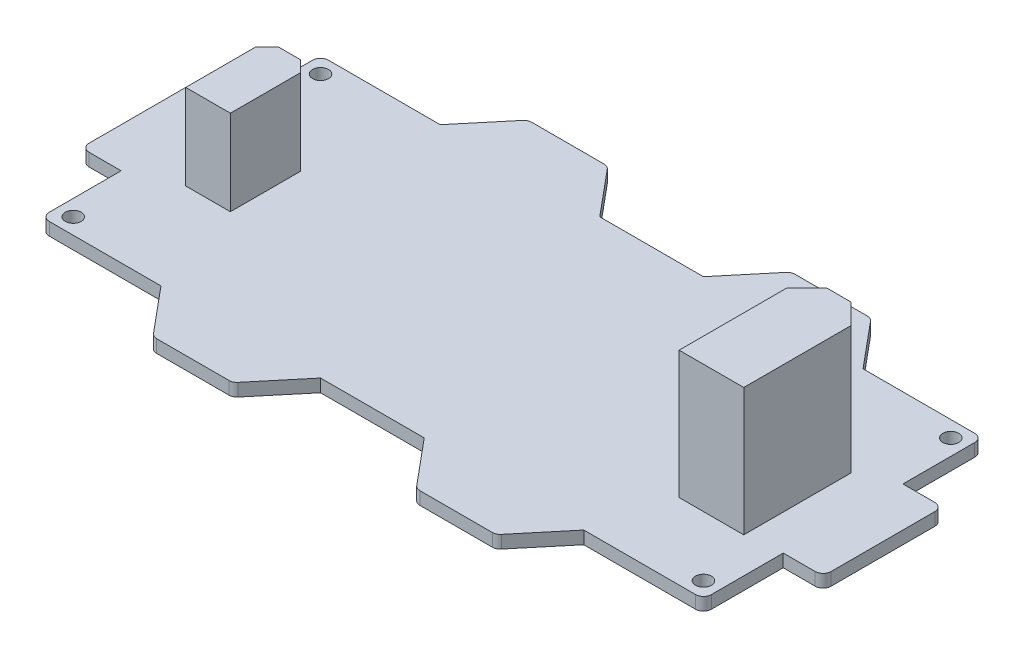
SolidWorks part; units mm, degrees
ref_plane "前视基准面" through (0, 0, 0) normal (0, 0, 1) x (1, 0, 0)
ref_plane "上视基准面" through (0, 0, 0) normal (0, 1, 0) x (1, 0, 0)
ref_plane "右视基准面" through (0, 0, 0) normal (1, 0, 0) x (0, 0, -1)
other "Configuration Table"
sketch "草图1" plane through (0, 0, 0) normal (0, 1, 0) x (1, 0, 0)
  line L0 (-26.5, 17.5) -> (-21.5, 23.5)
  line L1 (-41.5, -17.5) -> (-26.5, -17.5)
  line L2 (-41.5, -17.5) -> (-41.5, -7.5)
  line L3 (-41.5, 17.5) -> (-26.5, 17.5)
  line L4 (41.5, -17.5) -> (41.5, 17.5) construction
  line L5 (0, 17.5) -> (0, -17.5) construction
  line L6 (-41.5, 0) -> (41.5, 0) construction
  line L7 (-21.5, 23.5) -> (-11.5, 23.5)
  line L8 (-11.5, 23.5) -> (-6.5, 17.5)
  line L9 (-11.5, -23.5) -> (-6.5, -17.5)
  line L10 (-21.5, -23.5) -> (-11.5, -23.5)
  line L11 (-26.5, -17.5) -> (-21.5, -23.5)
  line L12 (21.5, -23.5) -> (11.5, -23.5)
  line L13 (11.5, -23.5) -> (6.5, -17.5)
  line L14 (26.5, -17.5) -> (21.5, -23.5)
  line L15 (11.5, 23.5) -> (6.5, 17.5)
  line L16 (21.5, 23.5) -> (11.5, 23.5)
  line L17 (26.5, 17.5) -> (21.5, 23.5)
  line L18 (-6.5, 17.5) -> (6.5, 17.5)
  line L19 (26.5, 17.5) -> (41.5, 17.5)
  line L20 (-6.5, -17.5) -> (6.5, -17.5)
  line L21 (26.5, -17.5) -> (41.5, -17.5)
  line L22 (-41.5, 7.5) -> (-41.5, 17.5)
  line L23 (-46.5, -7.5) -> (-41.5, -7.5)
  line L24 (-46.5, -7.5) -> (-46.5, 7.5)
  line L25 (-46.5, 7.5) -> (-41.5, 7.5)
  line L27 (-41.5, 7.5) -> (-41.5, -7.5) construction
  line L28 (-46.5, 0) -> (-36.5, 0) construction
  line L29 (46.5, 7.5) -> (41.5, 7.5)
  line L30 (46.5, -7.5) -> (41.5, -7.5)
  line L31 (46.5, -7.5) -> (46.5, 7.5)
  line L32 (41.5, -7.5) -> (41.5, -17.5)
  line L33 (41.5, 7.5) -> (41.5, 17.5)
  circle A0 centre (-39.5, 15.5) radius 1
  circle A1 centre (-39.5, -15.5) radius 1
  circle A2 centre (39.5, -15.5) radius 1
  circle A3 centre (39.5, 15.5) radius 1
  point P0 (0, 0)
  dimension "D9" = 2
  dimension "D1" = 15
  dimension "D2" = 35
  dimension "D3" = 20
  dimension "D4" = 5
  dimension "D5" = 6
  dimension "D6" = 10
  dimension "D7" = 15
  dimension "D8" = 83
  dimension "D10" = 2
  dimension "D11" = 2
extrude "PCB" add sketch "草图1" along normal blind 1.6
sketch "板上孔" plane through (0, 1.6, 0) normal (0, 1, 0) x (1, 0, 0)
  line L0 (0, -61.9012) -> (0, 61.9012) construction
  line L1 (-109.9353, 0) -> (109.9353, 0) construction
  line L2 (-14, -28) -> (14, -28) construction
  line L3 (-14, 33.5) -> (14, 33.5) construction
  line L4 (-14, 33.5) -> (-14, 22.5) construction
  line L5 (-14, 22.5) -> (14, 22.5) construction
  line L6 (14, 33.5) -> (14, 22.5) construction
  line L7 (0, 22.5) -> (0, 33.5) construction
  line L8 (-14, 28) -> (14, 28) construction
  line L9 (0, -22.5) -> (0, -33.5) construction
  line L10 (14, -33.5) -> (14, -22.5) construction
  line L11 (-14, -22.5) -> (14, -22.5) construction
  line L12 (-14, -33.5) -> (-14, -22.5) construction
  line L13 (-14, -33.5) -> (14, -33.5) construction
  line L14 (38, 0) -> (28, 0) construction
  line L15 (-38, -14) -> (-28, -14) construction
  line L16 (-38, -14) -> (-38, 14) construction
  line L17 (-38, 14) -> (-28, 14) construction
  line L18 (-28, -14) -> (-28, 14) construction
  line L19 (-33, 14) -> (-33, -14) construction
  line L20 (-38, 0) -> (-28, 0) construction
  line L21 (33, 14) -> (33, -14) construction
  line L22 (28, -14) -> (28, 14) construction
  line L23 (38, 14) -> (28, 14) construction
  line L24 (38, -14) -> (38, 14) construction
  line L25 (38, -14) -> (28, -14) construction
  point P0 (0, 28)
  point P4 (0, 0)
  point P7 (0, 0)
  point P19 (0, -28)
  point P20 (-33, 0)
  point P32 (33, 0)
  dimension "D1" = 28
  dimension "D2" = 11
  dimension "D3" = 22.5
  dimension "D4" = 10
  dimension "D5" = 28
  dimension "D6" = 28
sketch "草图3" plane through (0, 1.6, 0) normal (0, 1, 0) x (1, 0, 0)
  line L0 (28.95, 5.45) -> (31.5, 8)
  line L1 (37.05, -8) -> (28.95, -8)
  line L2 (37.05, -8) -> (37.05, 5.45)
  line L3 (34.5, 8) -> (31.5, 8)
  line L4 (28.95, -8) -> (28.95, 5.45)
  line L5 (33, 8) -> (33, -8) construction
  line L6 (37.05, 0) -> (28.95, 0) construction
  line L7 (37.05, 5.45) -> (34.5, 8)
  point P0 (33, 0)
  dimension "D1" = 16
  dimension "D2" = 8.1
  dimension "D4" = 1.5
  dimension "D5" = 3
extrude "XT60" add sketch "草图3" along normal blind 16
sketch "草图4" plane through (0, 1.6, 0) normal (0, 1, 0) x (1, 0, 0)
  line L0 (-34.4, 5.1) -> (-35.8, 3.7)
  line L1 (-30.2, -5.1) -> (-35.8, -5.1)
  line L2 (-30.2, -5.1) -> (-30.2, 3.7)
  line L3 (-31.6, 5.1) -> (-34.4, 5.1)
  line L4 (-35.8, -5.1) -> (-35.8, 3.7)
  line L5 (-33, 5.1) -> (-33, -5.1) construction
  line L6 (-30.2, 0) -> (-35.8, 0) construction
  line L7 (-30.2, 3.7) -> (-31.6, 5.1)
  point P0 (-33, 0)
  point P1 (-35.8, 5.1)
  point P3 (-30.2, 5.1)
  dimension "D1" = 10.2
  dimension "D2" = 5.6
extrude "XT30" add sketch "草图4" along normal blind 10.7
fillet "圆角2" radius 1 16 edges at (-41.5, 0.8, 17.5) (-21.5, 0.8, 23.5) (-11.5, 0.8, 23.5) (11.5, 0.8, 23.5) (21.5, 0.8, 23.5) (21.5, 0.8, -23.5) (11.5, 0.8, -23.5) (-11.5, 0.8, -23.5) (-21.5, 0.8, -23.5) (-46.5, 0.8, -7.5) (-41.5, 0.8, -17.5) (-46.5, 0.8, 7.5) (46.5, 0.8, 7.5) (46.5, 0.8, -7.5) (41.5, 0.8, -17.5) (41.5, 0.8, 17.5)
